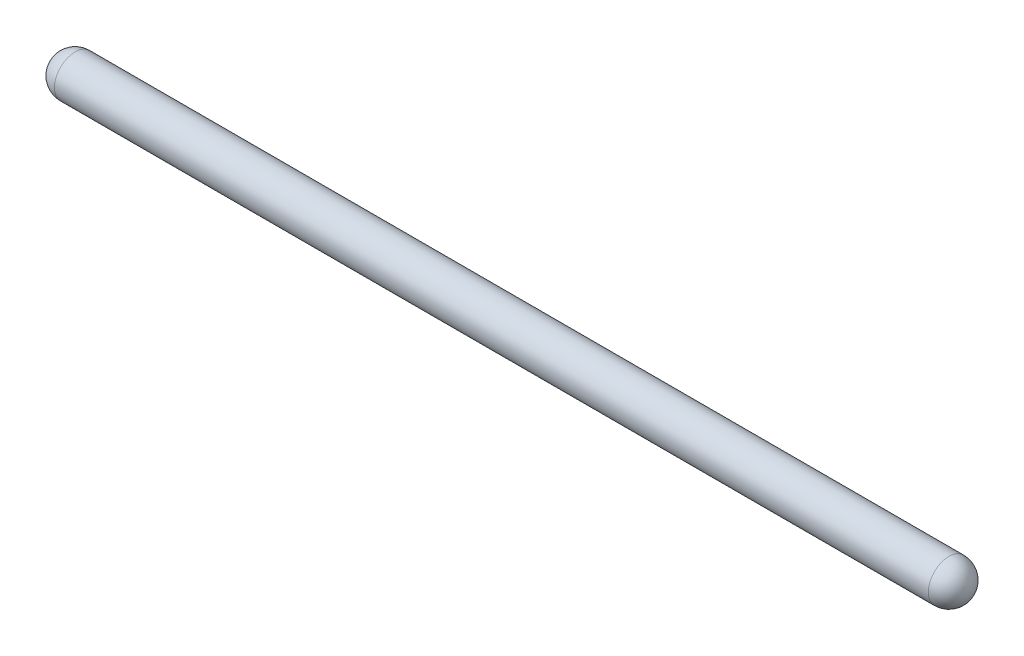
SolidWorks part; units mm, degrees
ref_plane "Front Plane" through (0, 0, 0) normal (0, 0, 1) x (1, 0, 0)
ref_plane "Top Plane" through (0, 0, 0) normal (0, 1, 0) x (1, 0, 0)
ref_plane "Right Plane" through (0, 0, 0) normal (1, 0, 0) x (0, 0, -1)
sketch "Sketch1" plane through (0, 0, 0) normal (0, 1, 0) x (1, 0, 0)
  circle A0 centre (0, 0) radius 1.5
  dimension "D1" = 3
sketch "Sketch2" plane through (0, 0, 0) normal (0, 0, 1) x (1, 0, 0)
  line L0 (0, 0) -> (63.5, 0) construction
  line L1 (0, 1.5) -> (63.5, 1.5)
  line L3 (-1.5, 0) -> (65, 0)
  arc A0 (0, 1.5) -> (-1.5, 0) centre (0, 0) ccw
  arc A1 (65, 0) -> (63.5, 1.5) centre (63.5, 0) ccw
  point P3 (31.75, 0)
  dimension "D1" = 63.5
  dimension "D2" = 1.5
revolve "Revolve2" add sketch "Sketch2" angle 360 about L0
